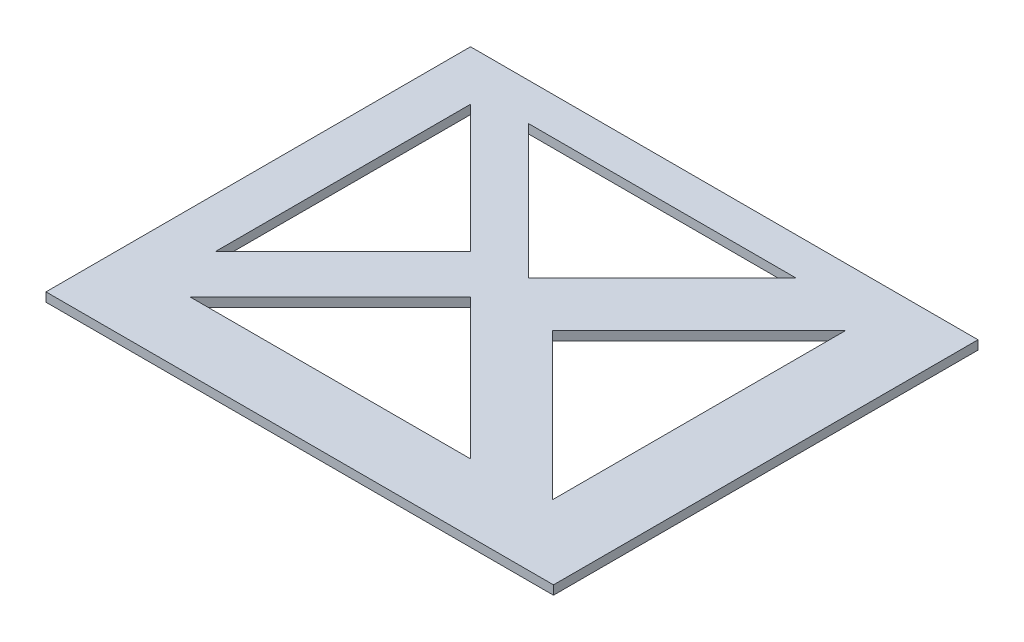
SolidWorks part; units mm, degrees
ref_plane "前视基准面" through (0, 0, 0) normal (0, 0, 1) x (1, 0, 0)
ref_plane "上视基准面" through (0, 0, 0) normal (0, 1, 0) x (1, 0, 0)
ref_plane "右视基准面" through (0, 0, 0) normal (1, 0, 0) x (0, 0, -1)
sketch "草图1" plane through (0, 0, 0) normal (0, 1, 0) x (1, 0, 0)
  line L0 (-124.5099, 163.0274) -> (-124.5099, 134.7432)
  line L1 (-130.0402, 168.5577) -> (-30.0402, 168.5577)
  line L2 (-130.0402, 168.5577) -> (-130.0402, 68.5577)
  line L3 (-130.0402, 68.5577) -> (-30.0402, 68.5577)
  line L4 (-30.0402, 168.5577) -> (-30.0402, 68.5577)
  line L5 (-130.0402, 168.5577) -> (-30.0402, 68.5577) construction
  line L6 (-130.0402, 68.5577) -> (-30.0402, 168.5577) construction
  line L7 (-124.5099, 134.7432) -> (-110.3677, 148.8853)
  line L8 (-110.3677, 148.8853) -> (-124.5099, 163.0274)
  line L9 (-119.4535, 164.3897) -> (-104.6043, 149.5405)
  line L10 (-104.6043, 149.5405) -> (-89.755, 164.3897)
  line L11 (-89.755, 164.3897) -> (-119.4535, 164.3897)
  line L12 (-105.9565, 144.4741) -> (-121.5129, 128.9178)
  line L13 (-121.5129, 128.9178) -> (-90.4002, 128.9178)
  line L14 (-90.4002, 128.9178) -> (-105.9565, 144.4741)
  line L15 (-81.9149, 162.0537) -> (-98.1784, 145.7902)
  line L16 (-98.1784, 145.7902) -> (-81.9149, 129.5268)
  line L17 (-81.9149, 162.0537) -> (-81.9149, 129.5268)
  point P0 (-80.0402, 118.5577)
  dimension "D1" = 100
  dimension "D2" = 100
  dimension "D3" = 20
  dimension "D4" = 21
  dimension "D5" = 22
  dimension "D6" = 23
  dimension "D7" = 23
extrude "凸台-拉伸1" add sketch "草图1" along normal blind 10
sketch "草图2" plane through (0, 10, 0) normal (0, 1, 0) x (1, 0, 0)
  line L0 (-130.0402, 121.407) -> (-73.6751, 121.407)
  line L1 (-130.0402, 168.5577) -> (-130.0402, 68.5577) construction
  line L2 (-73.6751, 121.407) -> (-73.6751, 168.5577)
  line L3 (-30.0402, 168.5577) -> (-130.0402, 168.5577) construction
  line L4 (-73.6751, 168.5577) -> (-30.0402, 168.5577)
  line L5 (-30.0402, 168.5577) -> (-30.0402, 68.5577)
  line L6 (-30.0402, 68.5577) -> (-130.0402, 68.5577)
  line L7 (-130.0402, 68.5577) -> (-130.0402, 121.407)
extrude "切除-拉伸1" cut sketch "草图2" against normal blind 10
sketch "草图3" plane through (0, 10, 0) normal (0, 1, 0) x (1, 0, 0)
  line L0 (-130.0402, 168.5577) -> (-73.6751, 168.5577)
  line L1 (-73.6751, 168.5577) -> (-73.6751, 121.407)
  line L2 (-73.6751, 121.407) -> (-130.0402, 121.407)
  line L3 (-130.0402, 121.407) -> (-130.0402, 168.5577)
extrude "切除-拉伸2" cut sketch "草图3" against normal blind 9
